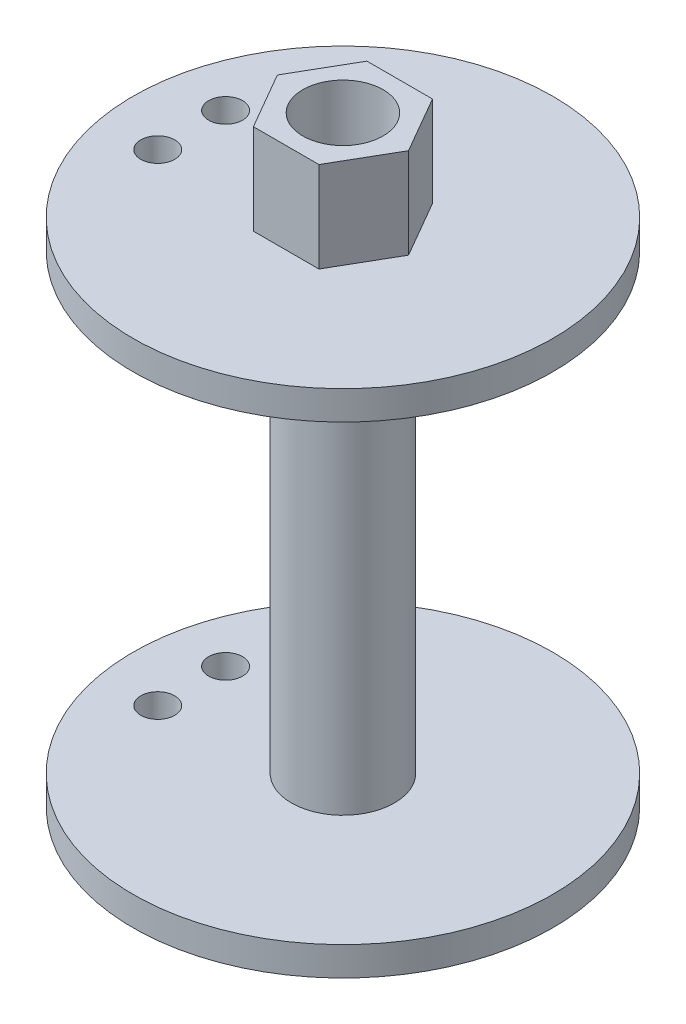
SolidWorks part; units mm, degrees
ref_plane "Front Plane" through (0, 0, 0) normal (0, 0, 1) x (1, 0, 0)
ref_plane "Top Plane" through (0, 0, 0) normal (0, 1, 0) x (1, 0, 0)
ref_plane "Right Plane" through (0, 0, 0) normal (1, 0, 0) x (0, 0, -1)
sketch "Sketch1" plane through (0, 0, 0) normal (0, 1, 0) x (1, 0, 0)
  circle A0 centre (0, 0) radius 3.175
  circle A1 centre (0, 0) radius 3.55
  circle A2 centre (0, 0) radius 18.55
  dimension "D1" = 6.35
  dimension "D2" = 0.375
  dimension "D3" = 15
extrude "Boss-Extrude1" add sketch "Sketch1" along normal blind 2.56 contours A2 A1
sketch "Sketch2" plane through (0, 2.56, 0) normal (0, 1, 0) x (1, 0, 0)
  circle A0 centre (0, 0) radius 3.55
  circle A1 centre (0, 0) radius 4.55
  dimension "D1" = 1
extrude "Boss-Extrude2" add sketch "Sketch2" along normal blind 20
mirror "Mirror1" about plane through (0, 22.56, 0) normal (0, 1, 0) of "Boss-Extrude2", "Boss-Extrude1"
sketch "Sketch5" plane through (0, 42.56, 0) normal (0, 1, 0) x (1, 0, 0)
  circle A0 centre (0, 0) radius 3.55
  circle A1 centre (0, 0) radius 18.55
extrude "Boss-Extrude3" add sketch "Sketch5" along normal blind 2.56
sketch "Sketch6" plane through (0, 45.12, 0) normal (0, 1, 0) x (1, 0, 0)
  line L1 (-5.795, 0) -> (-2.8975, -5.0186)
  line L2 (-2.8975, -5.0186) -> (2.8975, -5.0186)
  line L3 (2.8975, -5.0186) -> (5.795, 0)
  line L4 (5.795, 0) -> (2.8975, 5.0186)
  line L5 (2.8975, 5.0186) -> (-2.8975, 5.0186)
  line L6 (-2.8975, 5.0186) -> (-5.795, 0)
  circle A0 centre (0, 0) radius 5.0186 construction
  circle A1 centre (0, 0) radius 3.55
extrude "Boss-Extrude4" add sketch "Sketch6" along normal blind 8
sketch "Sketch7" plane through (0, 0, 0) normal (0, -1, 0) x (1, 0, 0)
  circle A0 centre (-13.3712, 0) radius 1.5
  circle A1 centre (-13.3712, -3) radius 1.5
  circle A2 centre (-13.3712, 3) radius 1.5
  dimension "D1" = 3
  dimension "D3" = 3
  dimension "D4" = 3
  dimension "D2" = 13.3712
extrude "Cut-Extrude1" cut sketch "Sketch7" against normal through all both and the other way through all contours A1 | A2
